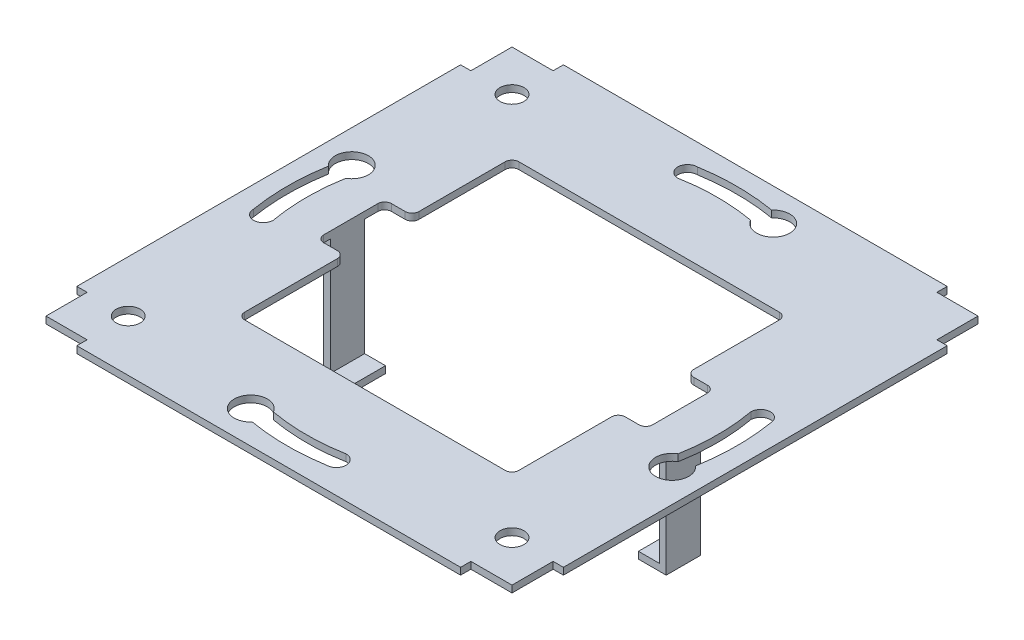
SolidWorks part; units mm, degrees
ref_plane "Спереди" through (0, 0, 0) normal (0, 0, 1) x (1, 0, 0)
ref_plane "Сверху" through (0, 0, 0) normal (0, 1, 0) x (1, 0, 0)
ref_plane "Справа" through (0, 0, 0) normal (1, 0, 0) x (0, 0, -1)
sketch "Эскиз2" plane through (0, 0, 0) normal (0, 1, 0) x (1, 0, 0)
  line L0 (-35.5, 28) -> (-35.5, -28)
  line L1 (28, -35.5) -> (-28, -35.5)
  line L3 (28, 35.5) -> (-28, 35.5)
  line L5 (28, -35.5) -> (-28, 35.5) construction
  line L6 (28, 35.5) -> (-28, -35.5) construction
  line L7 (35.5, 28) -> (35.5, -28)
  line L8 (-34, 34) -> (-28, 34)
  line L9 (28, 34) -> (34, 34)
  line L10 (34, 28) -> (34, 34)
  line L11 (34, -28) -> (34, -34)
  line L12 (28, -34) -> (34, -34)
  line L13 (-34, -34) -> (-28, -34)
  line L14 (-34, -28) -> (-34, -34)
  line L15 (-34, 28) -> (-34, 34)
  line L16 (28, 34) -> (28, 35.5)
  line L17 (34, 28) -> (35.5, 28)
  line L18 (34, -28) -> (35.5, -28)
  line L19 (28, -35.5) -> (28, -34)
  line L20 (-28, -34) -> (-28, -35.5)
  line L21 (-35.5, -28) -> (-34, -28)
  line L22 (-35.5, 28) -> (-34, 28)
  line L23 (-28, 35.5) -> (-28, 34)
  line L24 (20, 19) -> (20, 6.5255)
  line L29 (20, -19) -> (20, -5.4745)
  line L30 (21, 5.5255) -> (23, 5.5255)
  line L31 (21, -4.4745) -> (23, -4.4745)
  line L32 (24, 4.5255) -> (24, -3.4745)
  line L33 (-20, 19) -> (-20, 6.4181)
  line L34 (-20, -19) -> (-20, -5.4745)
  line L35 (-21, -4.4745) -> (-23, -4.4745)
  line L36 (-24, -3.4745) -> (-24, 4.4181)
  line L37 (-23, 5.4181) -> (-21, 5.4181)
  line L38 (0, 0) -> (-29.5317, 5.2802) construction
  line L39 (0, 0) -> (5.2802, 29.5317) construction
  line L40 (0, 0) -> (28, -28) construction
  line L41 (0, 0) -> (-28, -28) construction
  line L42 (-19, 20) -> (19, 20)
  line L43 (-19, -20) -> (19, -20)
  arc A4 (-20, 6.4181) -> (-21, 5.4181) centre (-21, 6.4181) cw
  arc A5 (-20, -5.4745) -> (-21, -4.4745) centre (-21, -5.4745) ccw
  arc A6 (20, -5.4745) -> (21, -4.4745) centre (21, -5.4745) cw
  arc A7 (20, 6.5255) -> (21, 5.5255) centre (21, 6.5255) ccw
  arc A8 (-24, 4.4181) -> (-23, 5.4181) centre (-23, 4.4181) cw
  arc A9 (-23, -4.4745) -> (-24, -3.4745) centre (-23, -3.4745) cw
  arc A10 (23, -4.4745) -> (24, -3.4745) centre (23, -3.4745) ccw
  arc A11 (23, 5.5255) -> (24, 4.5255) centre (23, 4.5255) cw
  arc A12 (-32.3752, -5.3289) -> (-32.3375, 5.5534) centre (0, 0) cw
  arc A13 (-29.5229, -5.3289) -> (-29.5317, 5.2802) centre (0, 0) cw
  arc A15 (-32.3375, 5.5534) -> (-29.5317, 5.2802) centre (-30.7442, 7.3717) cw
  arc A16 (-32.3752, -5.3289) -> (-29.5229, -5.3289) centre (-30.9491, -5.3289) ccw
  arc A17 (5.5534, 32.3375) -> (5.2802, 29.5317) centre (7.3717, 30.7442) cw
  arc A18 (-5.3289, 32.3752) -> (5.5534, 32.3375) centre (0, 0) cw
  arc A19 (-5.3289, 29.5229) -> (5.2802, 29.5317) centre (0, 0) cw
  arc A20 (-5.3289, 32.3752) -> (-5.3289, 29.5229) centre (-5.3289, 30.9491) ccw
  arc A21 (32.3375, -5.5534) -> (29.5317, -5.2802) centre (30.7442, -7.3717) cw
  arc A22 (32.3752, 5.3289) -> (32.3375, -5.5534) centre (0, 0) cw
  arc A23 (29.5229, 5.3289) -> (29.5317, -5.2802) centre (0, 0) cw
  arc A24 (32.3752, 5.3289) -> (29.5229, 5.3289) centre (30.9491, 5.3289) ccw
  arc A25 (-5.5534, -32.3375) -> (-5.2802, -29.5317) centre (-7.3717, -30.7442) cw
  arc A26 (5.3289, -32.3752) -> (-5.5534, -32.3375) centre (0, 0) cw
  arc A27 (5.3289, -29.5229) -> (-5.2802, -29.5317) centre (0, 0) cw
  arc A28 (5.3289, -32.3752) -> (5.3289, -29.5229) centre (5.3289, -30.9491) ccw
  circle A29 centre (28, -28) radius 1.75
  circle A32 centre (-28, -28) radius 1.75
  circle A33 centre (-28, 28) radius 1.75
  arc A34 (-20, -19) -> (-19, -20) centre (-19, -19) ccw
  arc A35 (20, -19) -> (19, -20) centre (19, -19) cw
  arc A36 (20, 19) -> (19, 20) centre (19, 19) ccw
  arc A37 (-20, 19) -> (-19, 20) centre (-19, 19) cw
  point P0 (0, 0)
  point P52 (-20, 5.4181)
  point P59 (20, 5.5255)
  dimension "D1" = 1
  dimension "D4" = 3
  dimension "D3" = 90
  dimension "D5" = 90
  dimension "D2" = 4
extrude "Бобышка-Вытянуть1" add sketch "Эскиз2" along normal blind 1
sketch "Эскиз3" plane through (0, 0, 0) normal (0, 0, 1) x (1, 0, 0)
  line L0 (-25, 0) -> (-24, 0)
  line L2 (-24, 0) -> (-24, -17)
  line L3 (-24, -17) -> (-20.9534, -17)
  line L4 (-20.9534, -17) -> (-20.9534, -18)
  line L5 (-20.9534, -18) -> (-25, -18)
  line L6 (-25, 0) -> (-25, -18)
  line L8 (0, 16.6146) -> (0, -8.6072) construction
  line L9 (25, 0) -> (25, -18)
  line L10 (20.9534, -18) -> (25, -18)
  line L11 (20.9534, -17) -> (20.9534, -18)
  line L12 (24, -17) -> (20.9534, -17)
  line L13 (24, 0) -> (24, -17)
  line L14 (25, 0) -> (24, 0)
  line L15 (-28, 0) -> (28, 0) construction
extrude "Бобышка-Вытянуть2" add sketch "Эскиз3" along normal mid plane 5
